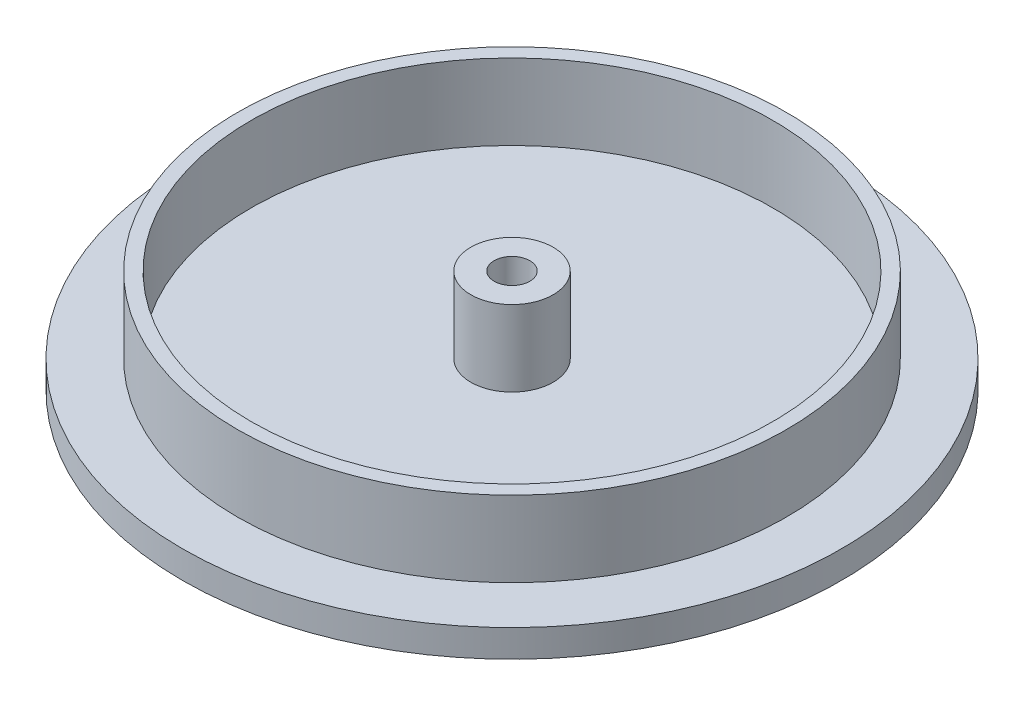
SolidWorks part; units mm, degrees
ref_plane "Front Plane" through (0, 0, 0) normal (0, 0, 1) x (1, 0, 0)
ref_plane "Top Plane" through (0, 0, 0) normal (0, 1, 0) x (1, 0, 0)
ref_plane "Right Plane" through (0, 0, 0) normal (1, 0, 0) x (0, 0, -1)
sketch "Sketch1" plane through (0, 0, 0) normal (0, 1, 0) x (1, 0, 0)
  circle A0 centre (0, 0) radius 60
  dimension "D1" = 120
extrude "Boss-Extrude1" add sketch "Sketch1" along normal blind 5 contours A0
sketch "Sketch2" plane through (0, 5, 0) normal (0, 1, 0) x (1, 0, 0)
  circle A0 centre (0, 0) radius 50
  dimension "D1" = 100
extrude "Boss-Extrude2" add sketch "Sketch2" along normal blind 13.8
sketch "Sketch3" plane through (0, 18.8, 0) normal (0, 1, 0) x (1, 0, 0)
  circle A0 centre (0, 0) radius 47.5
  dimension "D1" = 95
extrude "Cut-Extrude1" cut sketch "Sketch3" against normal blind 13.8
sketch "Sketch4" plane through (0, 5, 0) normal (0, 1, 0) x (1, 0, 0)
  circle A0 centre (0, 0) radius 7.5
  dimension "D1" = 15
extrude "Boss-Extrude3" add sketch "Sketch4" along normal blind 13.8
sketch "Sketch5" plane through (0, 18.8, 0) normal (0, 1, 0) x (1, 0, 0)
  circle A0 centre (0, 0) radius 3.25
  dimension "D1" = 6.5
sketch "Sketch6" plane through (0, 18.8, 0) normal (0, 1, 0) x (1, 0, 0)
  circle A1 centre (0, 0) radius 3.25
  circle A2 centre (0, 0) radius 3.25
  dimension "D1" = 0
extrude "Cut-Extrude2" cut sketch "Sketch6" against normal blind 35
